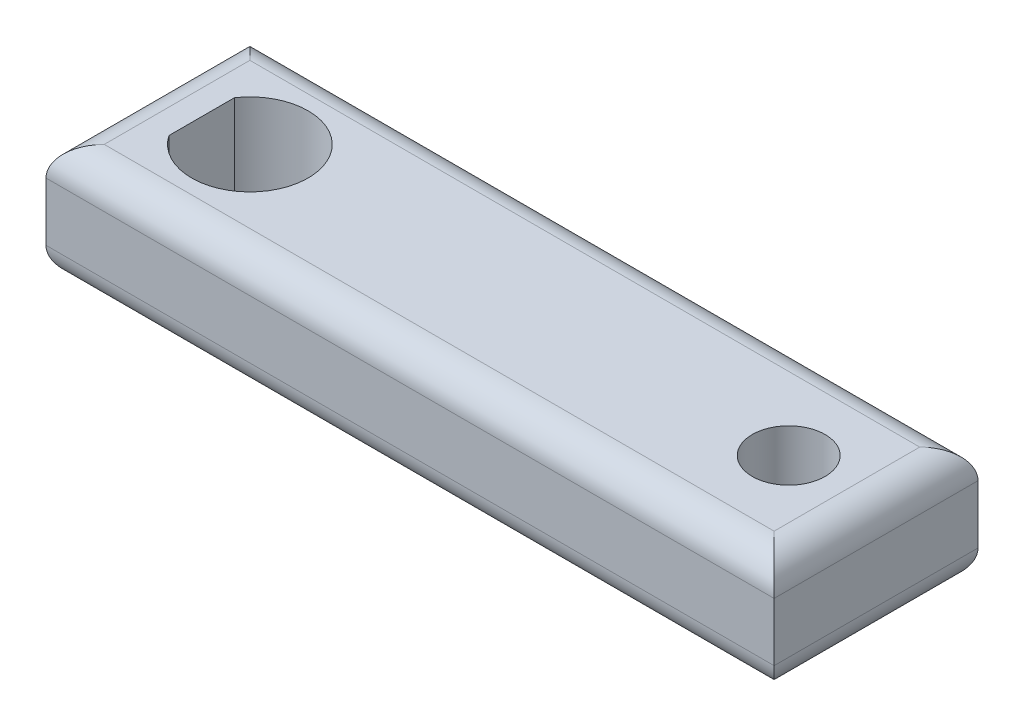
SolidWorks part; units mm, degrees
material "Malleable Cast Iron"
ref_plane "Front Plane" through (0, 0, 0) normal (0, 0, 1) x (1, 0, 0)
ref_plane "Top Plane" through (0, 0, 0) normal (0, 1, 0) x (1, 0, 0)
ref_plane "Right Plane" through (0, 0, 0) normal (1, 0, 0) x (0, 0, -1)
sketch "Sketch2" plane through (0, 0, 0) normal (0, 1, 0) x (1, 0, 0)
  line L1 (-25, 7) -> (25, 7)
  line L2 (-25, 7) -> (-25, -7)
  line L3 (-25, -7) -> (25, -7)
  line L4 (25, 7) -> (25, -7)
  line L5 (-25, 7) -> (25, -7) construction
  line L6 (-25, -7) -> (25, 7) construction
  point P0 (0, 0)
  dimension "D1" = 50
  dimension "D2" = 14
extrude "Boss-Extrude1" add sketch "Sketch2" along normal blind 8
sketch "Sketch3" plane through (0, 8, 0) normal (0, 1, 0) x (1, 0, 0)
  line L0 (-25, 7) -> (-25, -7) construction
  line L1 (-21.3072, 2.25) -> (-21.3072, -2.25)
  circle A0 centre (19, 0) radius 2.5
  arc A1 (-21.3072, -2.25) -> (-21.3072, 2.25) centre (-18, 0) ccw
  dimension "D1" = 5
  dimension "D2" = 8
  dimension "D3" = 4.5
  dimension "D4" = 19
  dimension "D5" = 7
extrude "Cut-Extrude2" cut sketch "Sketch3" against normal mid plane 18
fillet "Fillet5" radius 2 8 edges at (0, 8, 7) (-25, 8, 0) (0, 8, -7) (25, 8, 0) (0, 0, 7) (0, 0, -7) (25, 0, 0) (-25, 0, 0)
